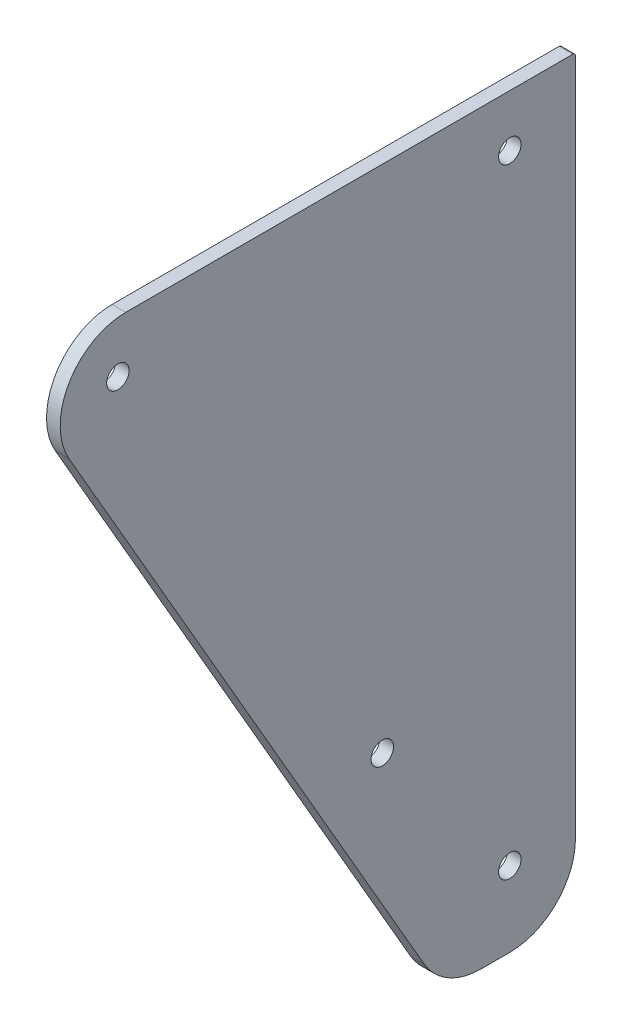
SolidWorks part; units mm, degrees
material "Galvanized Steel"
ref_plane "Front Plane" through (0, 0, 0) normal (0, 0, 1) x (1, 0, 0)
ref_plane "Top Plane" through (0, 0, 0) normal (0, 1, 0) x (1, 0, 0)
ref_plane "Right Plane" through (0, 0, 0) normal (1, 0, 0) x (0, 0, -1)
ref_plane "Plane1" through (0, 0, 0) normal (-1, 0, 0) x (0, -1, 0)
sketch "Sketch1" plane through (0, 0, 0) normal (-1, 0, 0) x (0, -1, 0)
  line L13 (-13, 31.3509) -> (-238, 161.2547)
  line L14 (-274, 140.4701) -> (-274, -23)
  line L15 (-273, -24) -> (-25, -24)
  line L16 (-1, 0) -> (-1, 10.5662)
  circle A4 centre (-255, 143.3568) radius 4.1
  circle A5 centre (-255, 0) radius 4.1
  arc A6 (-238, 161.2547) -> (-274, 140.4701) centre (-250, 140.4701) ccw
  arc A7 (-274, -23) -> (-273, -24) centre (-273, -23) ccw
  arc A8 (-25, -24) -> (-1, 0) centre (-25, 0) ccw
  arc A9 (-1, 10.5662) -> (-13, 31.3509) centre (-25, 10.5662) ccw
  circle A10 centre (-28.5, 0) radius 4.1
  circle A11 centre (-87.5, 46.6506) radius 4.1
extrude "Boss-Extrude1" add sketch "Sketch1" against normal blind 5
